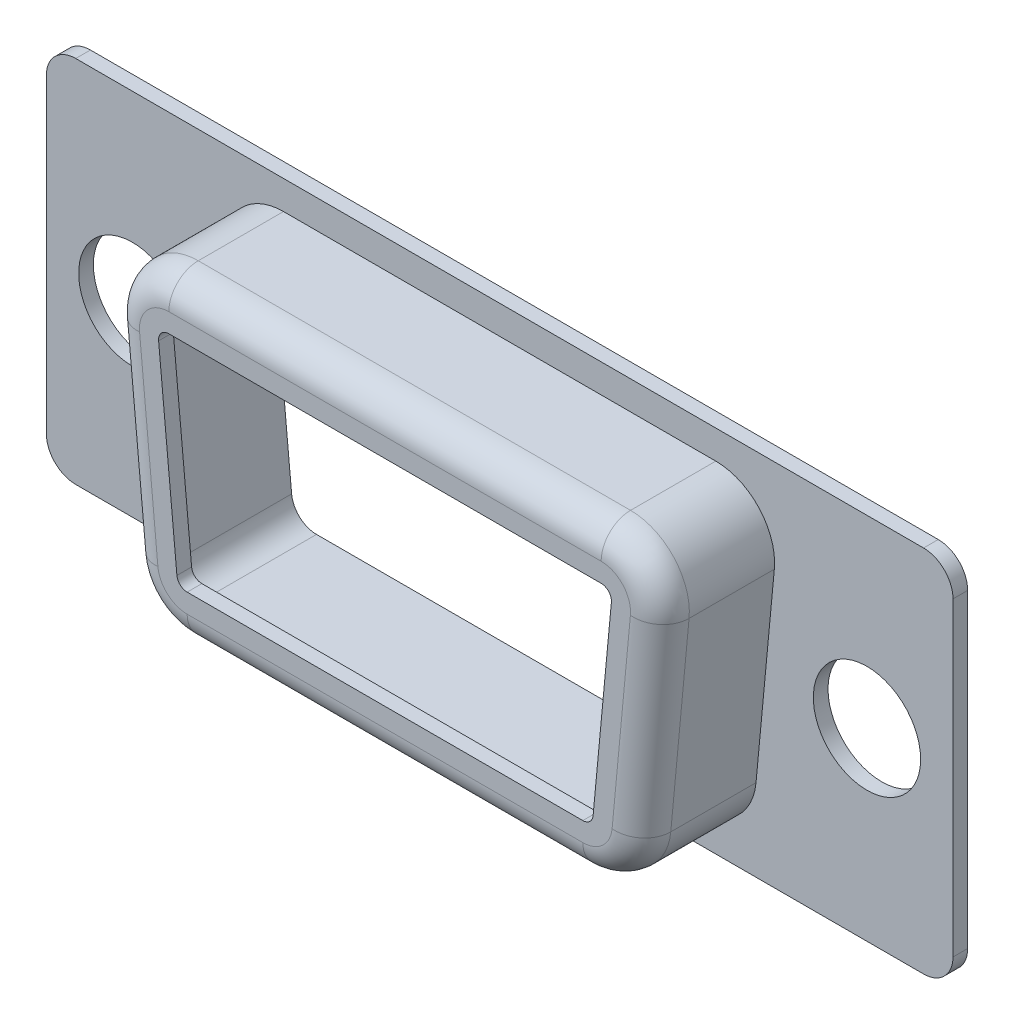
SolidWorks part; units mm, degrees
ref_plane "Front Plane" through (0, 0, 0) normal (0, 0, 1) x (1, 0, 0)
ref_plane "Top Plane" through (0, 0, 0) normal (0, 1, 0) x (1, 0, 0)
ref_plane "Right Plane" through (0, 0, 0) normal (1, 0, 0) x (0, 0, -1)
sketch "Sketch1" plane through (0, 0, 0) normal (0, 0, 1) x (1, 0, 0)
  line L1 (-14.42, 6.275) -> (14.42, 6.275)
  line L2 (-15.42, 5.275) -> (-15.42, -5.275)
  line L3 (-14.42, -6.275) -> (14.42, -6.275)
  line L4 (15.42, 5.275) -> (15.42, -5.275)
  line L5 (0, -6.275) -> (0, 6.275) construction
  line L6 (-15.42, 0) -> (15.42, 0) construction
  arc A0 (14.42, 6.275) -> (15.42, 5.275) centre (14.42, 5.275) cw
  arc A1 (15.42, -5.275) -> (14.42, -6.275) centre (14.42, -5.275) cw
  arc A2 (-15.42, -5.275) -> (-14.42, -6.275) centre (-14.42, -5.275) ccw
  arc A3 (-15.42, 5.275) -> (-14.42, 6.275) centre (-14.42, 5.275) cw
  point P0 (0, 0)
  point P6 (15.42, 6.275)
  point P10 (15.42, -6.275)
  point P15 (-15.42, 6.275)
  dimension "D3" = 1
  dimension "D1" = 30.84
  dimension "D2" = 12.55
extrude "Boss-Extrude1" add sketch "Sketch1" along normal blind 0.5
sketch "Sketch2" plane through (0, 0, 0.5) normal (0, 0, 1) x (1, 0, 0)
  line L0 (-15.42, 0) -> (15.42, 0) construction
  line L1 (-15.42, 5.275) -> (-15.42, -5.275) construction
  line L2 (15.42, -5.275) -> (15.42, 5.275) construction
  circle A0 centre (-12.495, 0) radius 1.825
  circle A1 centre (12.495, 0) radius 1.825
  dimension "D2" = 3.65
  dimension "D3" = 3.65
  dimension "D1" = 2.925
  dimension "D4" = 2.925
  dimension "D5" = 24.99
extrude "Cut-Extrude1" cut sketch "Sketch2" against normal up to surface (0.5 mm away) up to face at (0, 0, 0)
sketch "Sketch3" plane through (0, 0, 0.5) normal (0, 0, 1) x (1, 0, 0)
  line L0 (-15.42, 0) -> (15.42, 0) construction
  line L1 (-15.42, 5.275) -> (-15.42, -5.275) construction
  line L2 (15.42, -5.275) -> (15.42, 5.275) construction
  line L3 (-7.3524, 5.3) -> (7.3524, 5.3)
  line L4 (0, -6.275) -> (0, 6.275) construction
  line L5 (-14.42, -6.275) -> (14.42, -6.275) construction
  line L6 (14.42, 6.275) -> (-14.42, 6.275) construction
  line L7 (-6.7298, -5.3) -> (6.7298, -5.3)
  line L8 (9.55, 5.3) -> (9.55, -3.95) construction
  line L9 (-9.55, 5.3) -> (-9.55, -2.6) construction
  line L10 (9.3436, 3.1122) -> (8.721, -3.4878)
  line L11 (-9.3436, 3.1122) -> (-8.721, -3.4878)
  line L12 (-9.55, 5.3) -> (-9.55, 11.4186) construction
  circle A0 centre (-12.495, 0) radius 1.825 construction
  circle A1 centre (12.495, 0) radius 1.825 construction
  arc A2 (8.721, -3.4878) -> (6.7298, -5.3) centre (6.7298, -3.3) cw
  arc A3 (-6.7298, -5.3) -> (-8.721, -3.4878) centre (-6.7298, -3.3) cw
  arc A4 (9.3436, 3.1122) -> (7.3524, 5.3) centre (7.3524, 3.3) ccw
  arc A5 (-9.3436, 3.1122) -> (-7.3524, 5.3) centre (-7.3524, 3.3) cw
  point P14 (0, 5.3)
  point P18 (-9.0323, -0.1878)
  point P20 (9.0323, -0.1878)
  point P28 (8.55, -5.3)
  point P31 (-8.55, -5.3)
  dimension "D7" = 2
  dimension "D1" = 5.3
  dimension "D2" = 19.1
  dimension "D3" = 5.3
  dimension "D4" = 17.1
  dimension "D5" = 5.389
  dimension "D6" = 3.4678
  dimension "D8" = 3.4678
extrude "Boss-Extrude2" add sketch "Sketch3" along normal blind 3.9
sketch "Sketch4" plane through (0, 0, 4.4) normal (0, 0, 1) x (1, 0, 0)
  line L0 (7.0783, -3.3329) -> (7.7009, 3.2671)
  line L1 (7.3524, 3.65) -> (-7.3524, 3.65)
  line L2 (-7.7009, 3.2671) -> (-7.0783, -3.3329)
  line L3 (-6.7298, -3.65) -> (6.7298, -3.65)
  line L4 (8.721, -3.4878) -> (9.3436, 3.1122)
  line L5 (7.3524, 5.3) -> (-7.3524, 5.3)
  line L6 (-9.3436, 3.1122) -> (-8.721, -3.4878)
  line L7 (-6.7298, -5.3) -> (6.7298, -5.3)
  line L8 (8.721, -3.4878) -> (9.3436, 3.1122) construction
  line L9 (7.3524, 5.3) -> (-7.3524, 5.3) construction
  line L10 (-9.3436, 3.1122) -> (-8.721, -3.4878) construction
  line L11 (-6.7298, -5.3) -> (6.7298, -5.3) construction
  arc A0 (7.7009, 3.2671) -> (7.3524, 3.65) centre (7.3524, 3.3) ccw
  arc A1 (-7.3524, 3.65) -> (-7.7009, 3.2671) centre (-7.3524, 3.3) ccw
  arc A2 (-7.0783, -3.3329) -> (-6.7298, -3.65) centre (-6.7298, -3.3) ccw
  arc A3 (6.7298, -3.65) -> (7.0783, -3.3329) centre (6.7298, -3.3) ccw
  arc A4 (6.7298, -5.3) -> (8.721, -3.4878) centre (6.7298, -3.3) ccw
  arc A5 (9.3436, 3.1122) -> (7.3524, 5.3) centre (7.3524, 3.3) ccw
  arc A6 (-7.3524, 5.3) -> (-9.3436, 3.1122) centre (-7.3524, 3.3) ccw
  arc A7 (-8.721, -3.4878) -> (-6.7298, -5.3) centre (-6.7298, -3.3) ccw
  arc A8 (6.7298, -5.3) -> (8.721, -3.4878) centre (6.7298, -3.3) ccw construction
  arc A9 (9.3436, 3.1122) -> (7.3524, 5.3) centre (7.3524, 3.3) ccw construction
  arc A10 (-7.3524, 5.3) -> (-9.3436, 3.1122) centre (-7.3524, 3.3) ccw construction
  arc A11 (-8.721, -3.4878) -> (-6.7298, -5.3) centre (-6.7298, -3.3) ccw construction
  dimension "D1" = 0
  dimension "D2" = 1.65
extrude "Cut-Extrude2" cut sketch "Sketch4" against normal up to surface (4.4 mm away) up to face at (10.67, 0, 0)
ref_plane "Plane1" through (0, 0, 3.9) normal (0, 0, 1) x (1, 0, 0)
sketch "Sketch5" plane through (0, 0, 3.9) normal (0, 0, 1) x (1, 0, 0)
  line L0 (7.3524, 3.65) -> (-7.3524, 3.65) construction
  line L1 (-7.7009, 3.2671) -> (-7.0783, -3.3329) construction
  line L2 (-6.7298, -3.65) -> (6.7298, -3.65) construction
  line L3 (7.0783, -3.3329) -> (7.7009, 3.2671) construction
  line L4 (7.3524, 3.65) -> (-7.3524, 3.65)
  line L5 (-7.7009, 3.2671) -> (-7.0783, -3.3329)
  line L6 (-6.7298, -3.65) -> (6.7298, -3.65)
  line L7 (7.0783, -3.3329) -> (7.7009, 3.2671)
  line L8 (7.3524, 4.15) -> (-7.3524, 4.15)
  line L9 (-8.1987, 3.2202) -> (-7.576, -3.3798)
  line L10 (-6.7298, -4.15) -> (6.7298, -4.15)
  line L11 (7.576, -3.3798) -> (8.1987, 3.2202)
  arc A0 (-7.3524, 3.65) -> (-7.7009, 3.2671) centre (-7.3524, 3.3) ccw construction
  arc A1 (-7.0783, -3.3329) -> (-6.7298, -3.65) centre (-6.7298, -3.3) ccw construction
  arc A2 (6.7298, -3.65) -> (7.0783, -3.3329) centre (6.7298, -3.3) ccw construction
  arc A3 (7.7009, 3.2671) -> (7.3524, 3.65) centre (7.3524, 3.3) ccw construction
  arc A4 (-7.3524, 3.65) -> (-7.7009, 3.2671) centre (-7.3524, 3.3) ccw
  arc A5 (-7.0783, -3.3329) -> (-6.7298, -3.65) centre (-6.7298, -3.3) ccw
  arc A6 (6.7298, -3.65) -> (7.0783, -3.3329) centre (6.7298, -3.3) ccw
  arc A7 (7.7009, 3.2671) -> (7.3524, 3.65) centre (7.3524, 3.3) ccw
  arc A8 (-7.3524, 4.15) -> (-8.1987, 3.2202) centre (-7.3524, 3.3) ccw
  arc A9 (-7.576, -3.3798) -> (-6.7298, -4.15) centre (-6.7298, -3.3) ccw
  arc A10 (6.7298, -4.15) -> (7.576, -3.3798) centre (6.7298, -3.3) ccw
  arc A11 (8.1987, 3.2202) -> (7.3524, 4.15) centre (7.3524, 3.3) ccw
  dimension "D1" = 0.5
extrude "Cut-Extrude3" cut sketch "Sketch5" against normal up to surface (3.9 mm away) up to face at (0, -0.014, 0)
fillet "Fillet1" radius 1 8 edges at (8.076, -4.7791, 4.4) (0, -5.3, 4.4) (-8.076, -4.7791, 4.4) (-9.0323, -0.1878, 4.4) (-8.8316, 4.6462, 4.4) (0, 5.3, 4.4) (8.8316, 4.6462, 4.4) (9.0323, -0.1878, 4.4)
